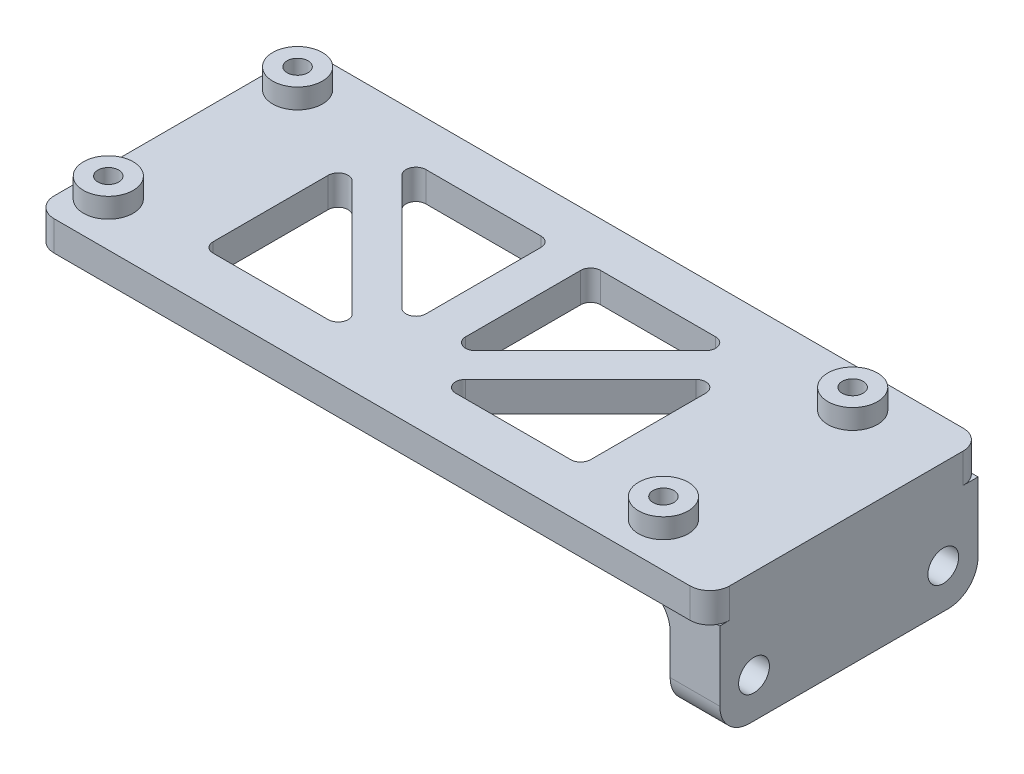
SolidWorks part; units mm, degrees
ref_plane "Front Plane" through (0, 0, 0) normal (0, 0, 1) x (1, 0, 0)
ref_plane "Top Plane" through (0, 0, 0) normal (0, 1, 0) x (1, 0, 0)
ref_plane "Right Plane" through (0, 0, 0) normal (1, 0, 0) x (0, 0, -1)
sketch "Sketch1" plane through (0, 0, 0) normal (0, 1, 0) x (1, 0, 0)
  line L1 (-31, 13.5) -> (37, 13.5)
  line L2 (-31, 13.5) -> (-31, -14)
  line L3 (-31, -14) -> (37, -14)
  line L4 (37, 13.5) -> (37, -14)
  dimension "D1" = 68
  dimension "D2" = 27.5
  dimension "D3" = 13.5
  dimension "D4" = 31
extrude "Boss-Extrude1" add sketch "Sketch1" along normal blind 3
sketch "Sketch2" plane through (0, 3, 0) normal (0, 1, 0) x (1, 0, 0)
  circle A0 centre (-28, 9.5) radius 2.5
  circle A1 centre (27.88, 9.5) radius 2.5
  circle A2 centre (27.88, -9.55) radius 2.5
  circle A3 centre (-28, -9.55) radius 2.5
  point P8 (0, 0)
  dimension "D1" = 5
  dimension "D2" = 5
  dimension "D3" = 5
  dimension "D4" = 5
  dimension "D5" = 55.88
  dimension "D6" = 19.05
  dimension "D7" = 55.88
  dimension "D8" = 19.05
  dimension "D9" = 28
  dimension "D10" = 9.5
  dimension "D11" = 9.5
  dimension "D12" = 28
fillet "Fillet1" radius 2 4 edges at (-31, 1.5, -13.5) (37, 1.5, -13.5) (37, 1.5, 14) (-31, 1.5, 14)
extrude "Boss-Extrude2" add sketch "Sketch2" along normal blind 2
sketch "Sketch4" plane through (0, 5, 0) normal (0, 1, 0) x (1, 0, 0)
  circle A0 centre (-28, 9.5) radius 1.05
  circle A1 centre (-28, -9.55) radius 1.05
  circle A2 centre (27.88, -9.55) radius 1.05
  circle A3 centre (27.88, 9.5) radius 1.05
  dimension "D1" = 2.1
  dimension "D2" = 2.1
  dimension "D3" = 2.1
  dimension "D4" = 2.1
extrude "Cut-Extrude2" cut sketch "Sketch4" against normal blind 12
sketch "Sketch5" plane through (0, 0, 0) normal (0, -1, 0) x (-1, 0, 0)
  line L1 (-32, -12.995) -> (-37, -12.995)
  line L2 (-32, -12.995) -> (-32, 12.995)
  line L3 (-32, 12.995) -> (-37, 12.995)
  line L4 (-37, -12.995) -> (-37, 12.995)
  line L5 (-32, -12.995) -> (-37, 12.995) construction
  line L6 (-32, 12.995) -> (-37, -12.995) construction
  point P0 (-34.5, 0)
  dimension "D1" = 34.5
  dimension "D2" = 0
  dimension "D3" = 5
extrude "Boss-Extrude3" add sketch "Sketch5" along normal blind 10
sketch "Sketch6" plane through (32, 0, 0) normal (-1, 0, 0) x (0, 0, 1)
  circle A0 centre (-9.5, -6) radius 1.55
  circle A1 centre (9.55, -6) radius 1.55
  dimension "D1" = 3.1
  dimension "D2" = 3.1
  dimension "D3" = 9.5
  dimension "D4" = 19.05
  dimension "D5" = 6
  dimension "D6" = 6
extrude "Cut-Extrude3" cut sketch "Sketch6" against normal blind 10
fillet "Fillet2" radius 3 2 edges at (34.5, -10, -12.995) (34.5, -10, 12.995)
fillet "Fillet3" radius 3 1 edges at (32, 0, 0)
sketch "Sketch7" plane through (0, 0, 0) normal (0, -1, 0) x (-1, 0, 0)
  line L0 (19, -9) -> (19, 6)
  line L1 (19, 6) -> (4, -9)
  line L2 (4, -9) -> (19, -9)
  line L3 (17, 9) -> (2, -6)
  line L4 (2, -6) -> (2, 9)
  line L5 (2, 9) -> (17, 9)
  point P16 (-2.1379, 19.1474)
  dimension "D1" = 15
  dimension "D2" = 15
  dimension "D3" = 15
  dimension "D8" = 2
  dimension "D9" = 9
  dimension "D10" = 9
  dimension "D11" = 19
extrude "Cut-Extrude4" cut sketch "Sketch7" against normal blind 10
fillet "Fillet4" radius 1 6 edges at (-19, 1.5, 9) (-4, 1.5, 9) (-19, 1.5, -6) (-17, 1.5, -9) (-2, 1.5, 6) (-2, 1.5, -9)
mirror "Mirror1" about plane through (0, 0, 0) normal (1, 0, 0) of "Fillet4", "Cut-Extrude4"
